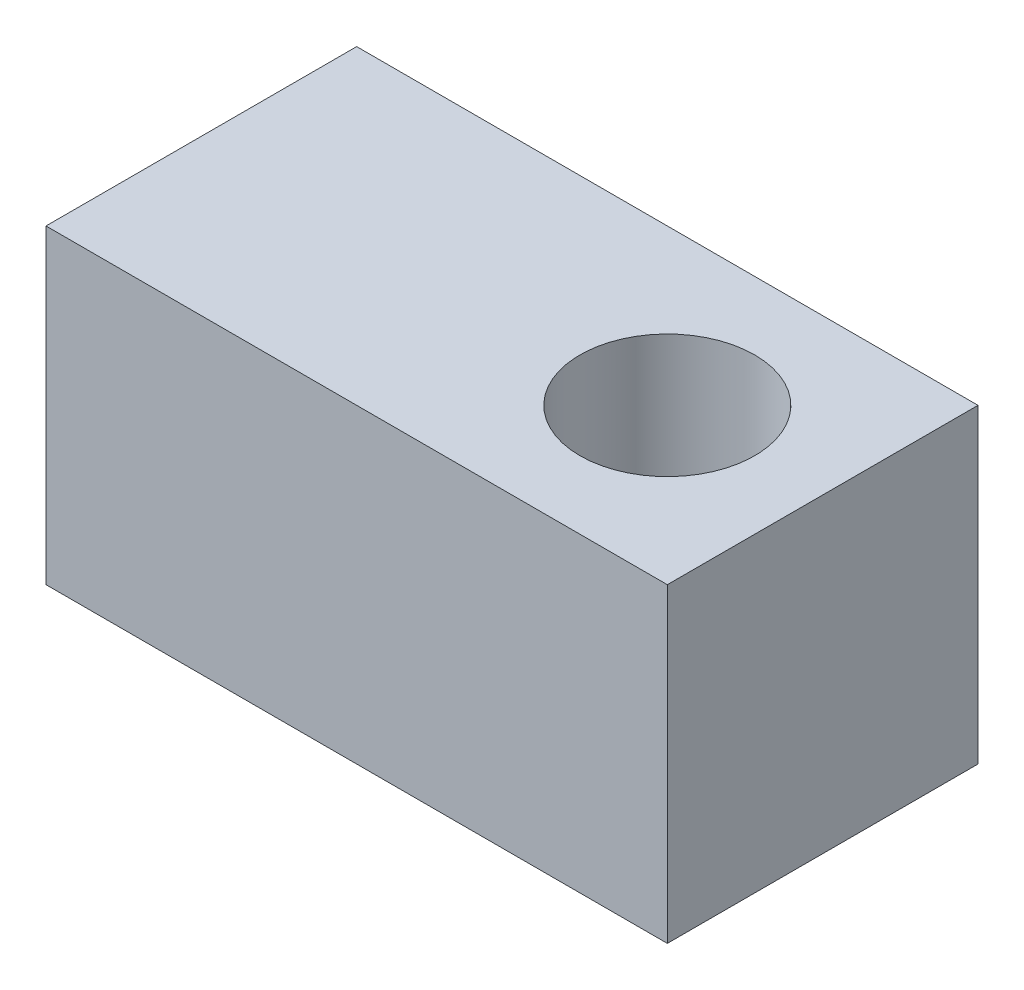
SolidWorks part; units mm, degrees
material "6061-T6 (SS)"
ref_plane "Front Plane" through (0, 0, 0) normal (0, 0, 1) x (1, 0, 0)
ref_plane "Top Plane" through (0, 0, 0) normal (0, 1, 0) x (1, 0, 0)
ref_plane "Right Plane" through (0, 0, 0) normal (1, 0, 0) x (0, 0, -1)
sketch "Sketch1" plane through (0, 0, 0) normal (0, 1, 0) x (1, 0, 0)
  line L1 (-50.8, -25.4) -> (50.8, -25.4)
  line L2 (-50.8, -25.4) -> (-50.8, 25.4)
  line L3 (-50.8, 25.4) -> (50.8, 25.4)
  line L4 (50.8, -25.4) -> (50.8, 25.4)
  line L5 (-50.8, -25.4) -> (50.8, 25.4) construction
  line L6 (-50.8, 25.4) -> (50.8, -25.4) construction
  point P0 (0, 0)
  dimension "D1" = 101.6
  dimension "D2" = 50.8
extrude "Boss-Extrude1" add sketch "Sketch1" along normal blind 50.8
sketch "Sketch2" plane through (0, 50.8, 0) normal (0, 1, 0) x (1, 0, 0)
  line L0 (-27.94, 0) -> (27.94, 0) construction
  line L1 (50.8, -25.4) -> (50.8, 25.4) construction
  circle A0 centre (25.4, 0) radius 14.2875
  point P2 (0, 0)
  dimension "D1" = 28.575
  dimension "D2" = 25.4
extrude "Cut-Extrude1" cut sketch "Sketch2" against normal up to next
hole_wizard "1/4-28 Tapped Hole1" positions "Sketch3" profile "Sketch4" tap size "1/4-28" standard "ANSI Inch"
sketch "Sketch3" plane through (0, 0, 0) normal (0, -1, 0) x (-1, 0, 0)
  line L0 (-27.94, 0) -> (27.94, 0) construction
  line L1 (50.8, 25.4) -> (50.8, -25.4) construction
  point P0 (44.45, 0)
  point P3 (0, 0)
  dimension "D1" = 6.35
sketch "Sketch4" plane through (-44.45, 0, 0) normal (1, 0, 0) x (0, 0, -1)
  line L0 (0, 0) -> (0, 29.7457)
  line L1 (0, 29.7457) -> (2.7051, 28.1203)
  line L2 (2.7051, 28.1203) -> (2.7051, 0)
  line L5 (2.7051, 0) -> (0, 0)
  line L10 (0, 29.7457) -> (-2.7051, 28.1203) construction
  line L11 (0, -6.35) -> (0, 107.95) construction
  dimension "Tap Drill Dia." = 5.4102
  dimension "Tap Drill Depth" = 28.1203
  dimension "Drill Angle" = 118
cosmetic thread "Hole Thread1"
